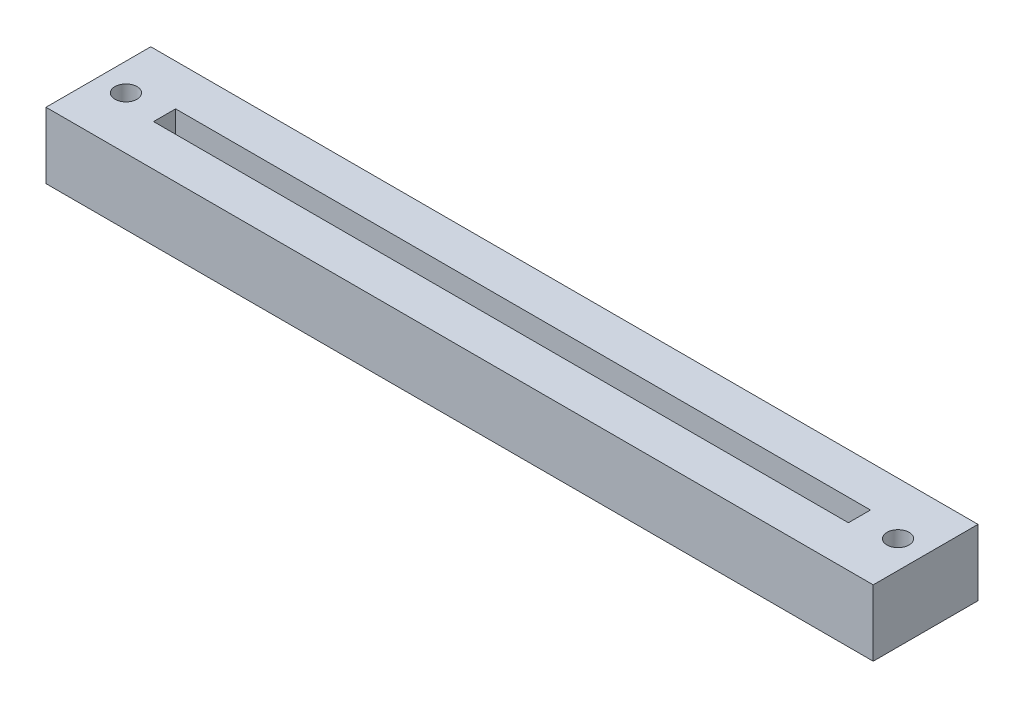
SolidWorks part; units mm, degrees
ref_plane "Front Plane" through (0, 0, 0) normal (0, 0, 1) x (1, 0, 0)
ref_plane "Top Plane" through (0, 0, 0) normal (0, 1, 0) x (1, 0, 0)
ref_plane "Right Plane" through (0, 0, 0) normal (1, 0, 0) x (0, 0, -1)
sketch "Sketch1" plane through (0, 0, 0) normal (0, 1, 0) x (1, 0, 0)
  line L1 (0, 0) -> (75, 0)
  line L2 (0, 0) -> (0, 9.5)
  line L3 (0, 9.5) -> (75, 9.5)
  line L4 (75, 0) -> (75, 9.5)
  dimension "D1" = 9.5
  dimension "D2" = 75
extrude "Boss-Extrude1" add sketch "Sketch1" along normal blind 6
sketch "Sketch2" plane through (0, 6, 0) normal (0, 1, 0) x (1, 0, 0)
  line L0 (0, 4.75) -> (75, 4.75) construction
  line L1 (0, 9.5) -> (0, 0) construction
  line L2 (75, 0) -> (75, 9.5) construction
  line L3 (37.5, 5.75) -> (37.5, 4.75) construction
  line L4 (6, 5.75) -> (69, 5.75)
  line L5 (6, 5.75) -> (6, 3.75)
  line L6 (6, 3.75) -> (69, 3.75)
  line L7 (69, 5.75) -> (69, 3.75)
  circle A0 centre (2.5, 4.75) radius 1
  circle A1 centre (72.5, 4.75) radius 1
  point P14 (6, 4.75)
  point P15 (37.5, 5.75)
  point P16 (37.5, 4.75)
  dimension "D1" = 2
  dimension "D2" = 2.5
  dimension "D3" = 2.5
  dimension "D4" = 63
  dimension "D5" = 2
extrude "Cut-Extrude1" cut sketch "Sketch2" against normal blind 3
